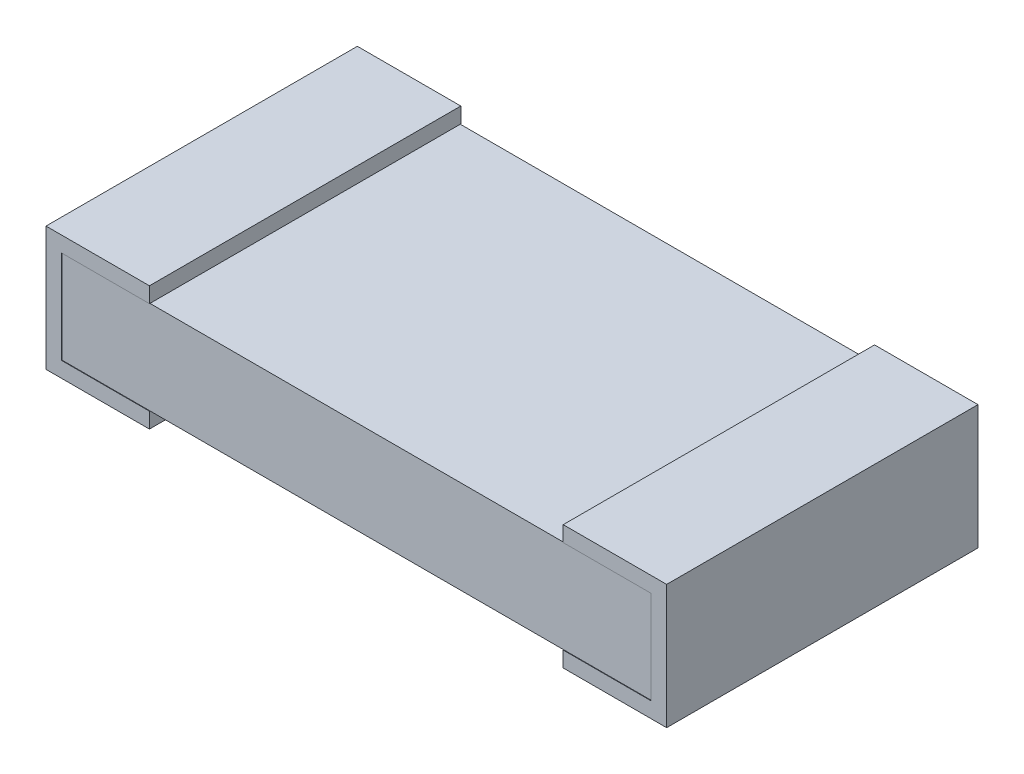
SolidWorks part; units mm, degrees
ref_plane "Front Plane" through (0, 0, 0) normal (0, 0, 1) x (1, 0, 0)
ref_plane "Top Plane" through (0, 0, 0) normal (0, 1, 0) x (1, 0, 0)
ref_plane "Right Plane" through (0, 0, 0) normal (1, 0, 0) x (0, 0, -1)
sketch "Sketch1" plane through (0, 0, 0) normal (0, 0, 1) x (1, 0, 0)
  line L0 (2.9718, 0.0762) -> (0.0762, 0.0762)
  line L1 (2.9718, 0.0762) -> (2.9718, 0.5334)
  line L2 (0.0762, 0.5334) -> (2.9718, 0.5334)
  line L3 (0.0762, 0.5334) -> (0.0762, 0.0762)
  dimension "D1" = 2.8956
  dimension "D2" = 0.4572
  dimension "D3" = 0.0762
  dimension "D4" = 0.0762
extrude "Base-Extrude" add sketch "Sketch1" against normal mid plane 1.524
ref_plane "Plane1" through (0, 0, -0.7645) normal (0, 0, -1) x (-1, 0, 0)
sketch "Sketch2" plane through (0, 0, -0.7645) normal (0, 0, -1) x (-1, 0, 0)
  line L0 (0, 0) -> (-0.508, 0)
  line L1 (0, 0) -> (0, 0.6096)
  line L2 (0, 0.6096) -> (-0.508, 0.6096)
  line L3 (-0.508, 0.6096) -> (-0.508, 0.5334)
  line L4 (-2.9718, 0.5334) -> (-0.0762, 0.5334) construction
  line L5 (-0.508, 0) -> (-0.508, 0.0762)
  line L6 (-0.0762, 0.0762) -> (-2.9718, 0.0762) construction
  line L7 (-0.0762, 0.5334) -> (-0.0762, 0.0762) construction
  line L8 (-0.0762, 0.0762) -> (-0.508, 0.0762)
  line L9 (-0.508, 0.5334) -> (-0.0762, 0.5334)
  line L10 (-0.0762, 0.5334) -> (-0.0762, 0.0762)
  dimension "D1" = 0.508
  dimension "D2" = 0.508
  dimension "D3" = 0.0762
extrude "Boss-Extrude1" add sketch "Sketch2" against normal blind 1.5291
ref_plane "Plane2" through (1.524, 0, 0) normal (1, 0, 0) x (0, 0, -1)
mirror "Mirror1" about plane through (1.524, 0, 0) normal (1, 0, 0) of "Boss-Extrude1"
sketch "Component_Outline" plane through (0, 0, 0) normal (0, 1, 0) x (1, 0, 0)
  line L1 (0, -0.7645) -> (3.048, -0.7645)
  line L2 (0, -0.7645) -> (0, 0.7645)
  line L3 (0, 0.7645) -> (3.048, 0.7645)
  line L4 (3.048, -0.7645) -> (3.048, 0.7645)
